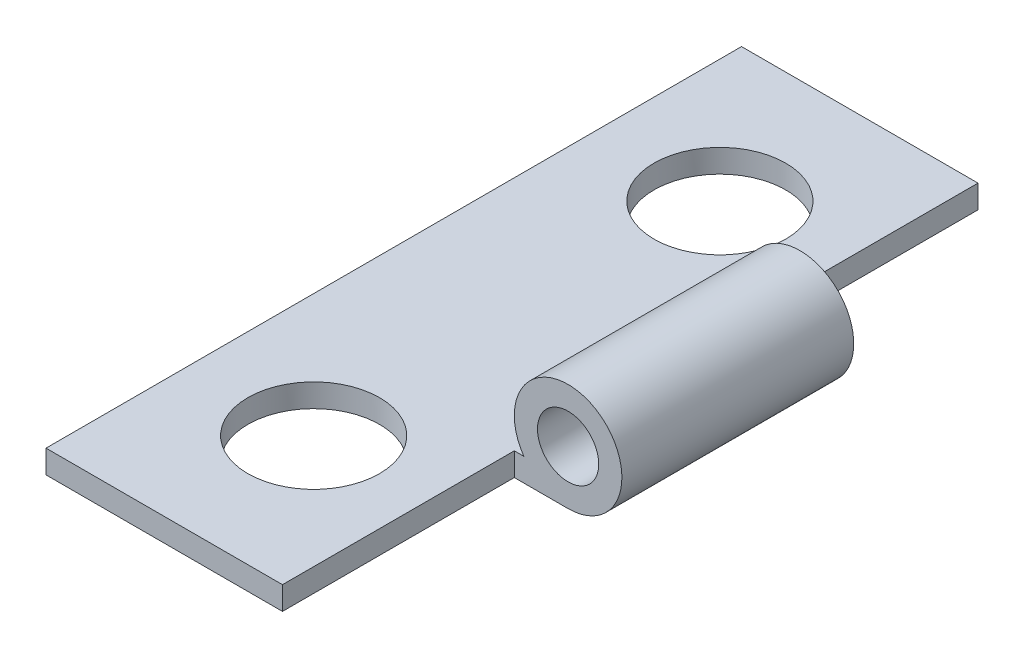
SolidWorks part; units mm, degrees
ref_plane "Front Plane" through (0, 0, 0) normal (0, 0, 1) x (1, 0, 0)
ref_plane "Top Plane" through (0, 0, 0) normal (0, 1, 0) x (1, 0, 0)
ref_plane "Right Plane" through (0, 0, 0) normal (1, 0, 0) x (0, 0, -1)
sketch "Sketch1" plane through (0, 0, 0) normal (0, 0, 1) x (1, 0, 0)
  line L4 (-1.5423, 2.9903) -> (-1.5423, 1.6367) construction
  line L5 (-1.5423, 1.6367) -> (-1.5423, -4.5326) construction
  line L6 (-11.0349, 1.6367) -> (-11.0349, 2.2717)
  line L7 (-11.0349, 2.2717) -> (-4.2962, 2.2717)
  line L8 (-11.0349, 1.6367) -> (-3.0847, 1.6367)
  circle A2 centre (-3.0847, 3.1099) radius 0.8382
  arc A3 (-3.0847, 1.6367) -> (-4.2962, 2.2717) centre (-3.0847, 3.1099) ccw
  point P11 (-7.9502, 1.6367)
  point P17 (-7.9502, 2.4317)
  point P18 (-1.5423, 2.9903)
  dimension "D2" = 1.6764
  dimension "D3" = 1.4732
  dimension "D1" = 7.9502
  dimension "D4" = 0.635
extrude "Boss-Extrude1" add sketch "Sketch1" along normal blind 19.05
sketch "Sketch2" plane through (0, 2.2717, 0) normal (0, 1, 0) x (1, 0, 0)
  line L0 (-4.5579, 0) -> (-4.5579, -19.05) construction
  line L1 (-4.5579, -6.35) -> (-1.6115, -6.35)
  line L2 (-4.5579, -6.35) -> (-4.5579, 0)
  line L3 (-4.5579, 0) -> (-1.6115, 0)
  line L4 (-1.6115, -6.35) -> (-1.6115, 0)
  line L5 (-4.2962, 0) -> (-11.0349, 0) construction
  line L6 (-1.6115, -19.05) -> (-4.5579, -19.05)
  line L7 (-1.6115, -19.05) -> (-1.6115, -12.7)
  line L8 (-1.6115, -12.7) -> (-4.5579, -12.7)
  line L9 (-4.5579, -19.05) -> (-4.5579, -12.7)
  circle A0 centre (-7.6655, -3.9624) radius 1.8034
  circle A1 centre (-7.6655, -15.0876) radius 1.8034
  dimension "D1" = 3.6068
  dimension "D2" = 3.6068
  dimension "D3" = 6.35
  dimension "D4" = 6.35
  dimension "D5" = 11.1252
  dimension "D6" = 3.9624
extrude "Cut-Extrude1" cut sketch "Sketch2" against normal blind 127 from offset 76.2
